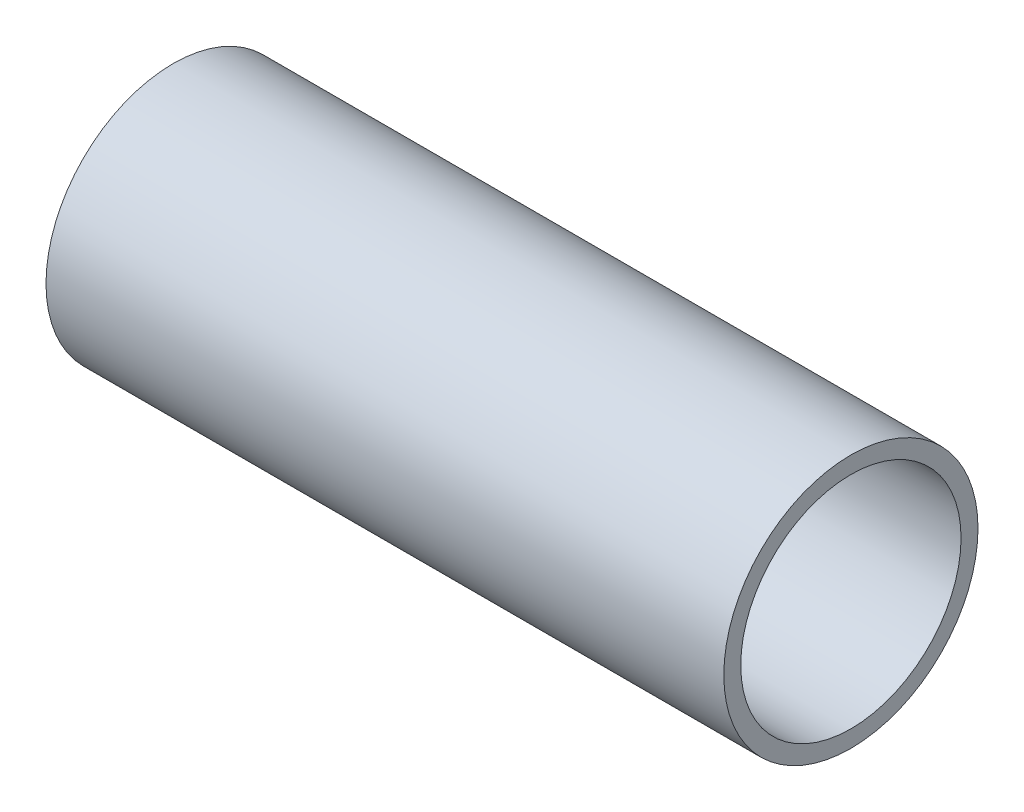
SolidWorks part; units mm, degrees
material "ПК/АБС"
ref_plane "Спереди" through (0, 0, 0) normal (0, 0, 1) x (1, 0, 0)
ref_plane "Сверху" through (0, 0, 0) normal (0, 1, 0) x (1, 0, 0)
ref_plane "Справа" through (0, 0, 0) normal (1, 0, 0) x (0, 0, -1)
sketch "Эскиз1" plane through (0, 0, 0) normal (1, 0, 0) x (0, 0, -1)
  circle A0 centre (0, 0) radius 22.5
  circle A1 centre (0, 0) radius 19.5
  dimension "D1" = 45
  dimension "D2" = 39
extrude "Бобышка-Вытянуть1" add sketch "Эскиз1" along normal blind 120
